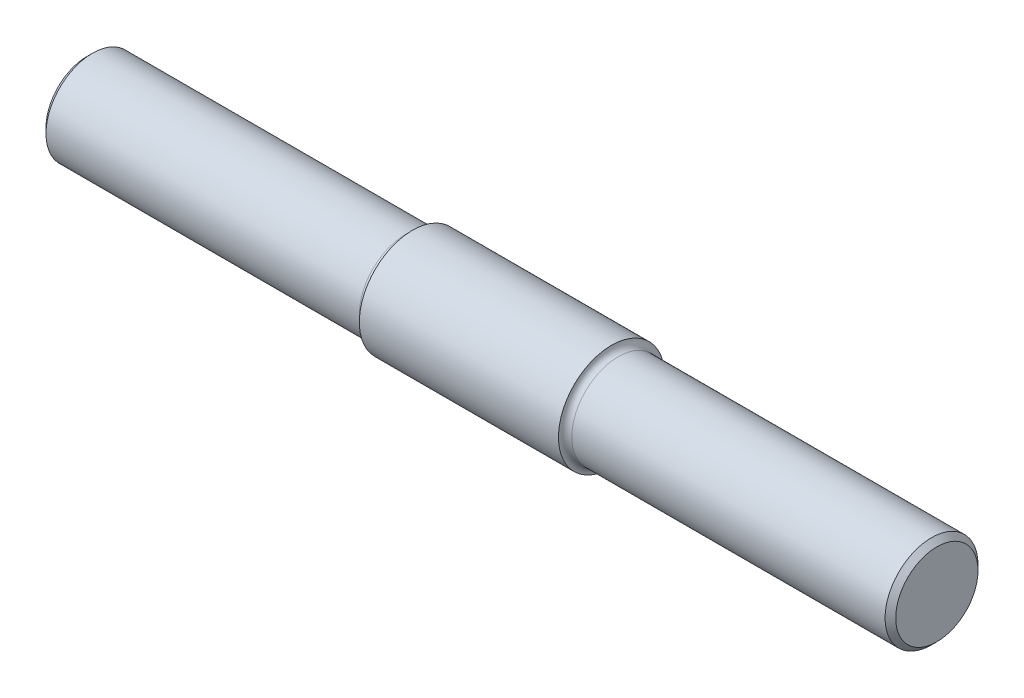
SolidWorks part; units mm, degrees
ref_plane "Front" through (0, 0, 0) normal (0, 0, 1) x (1, 0, 0)
ref_plane "Top" through (0, 0, 0) normal (0, 1, 0) x (1, 0, 0)
ref_plane "Right" through (0, 0, 0) normal (1, 0, 0) x (0, 0, -1)
sketch "Sketch1" plane through (0, 0, 0) normal (0, 0, 1) x (1, 0, 0)
  line L0 (-50.8, 0) -> (50.8, 0)
  line L1 (-50.8, 0) -> (-50.8, 5.5563)
  line L2 (-50.8, 5.5563) -> (-12.7, 5.5563)
  line L3 (-11.9062, 6.35) -> (11.9062, 6.35)
  line L4 (12.7, 5.5562) -> (50.8, 5.5563)
  line L5 (50.8, 5.5563) -> (50.8, 0)
  line L6 (0, 0) -> (0, 6.35) construction
  line L7 (-50.8, 0) -> (-80.9821, 0) construction
  arc A0 (-12.7, 5.5563) -> (-11.9062, 6.35) centre (-12.7, 6.35) ccw
  arc A1 (11.9062, 6.35) -> (12.7, 5.5562) centre (12.7, 6.35) ccw
  dimension "D1" = 11.1125
  dimension "D2" = 101.6
  dimension "D3" = 25.4
  dimension "D4" = 12.7
revolve "Revolve1" add sketch "Sketch1" angle 360 about L7
cosmetic thread "Cosmetic Thread1"
cosmetic thread "Cosmetic Thread2"
chamfer "Chamfer1" distance 0.635 angle 45 2 edges at (50.8, 0, -5.5563) (-50.8, 0, -5.5563)
